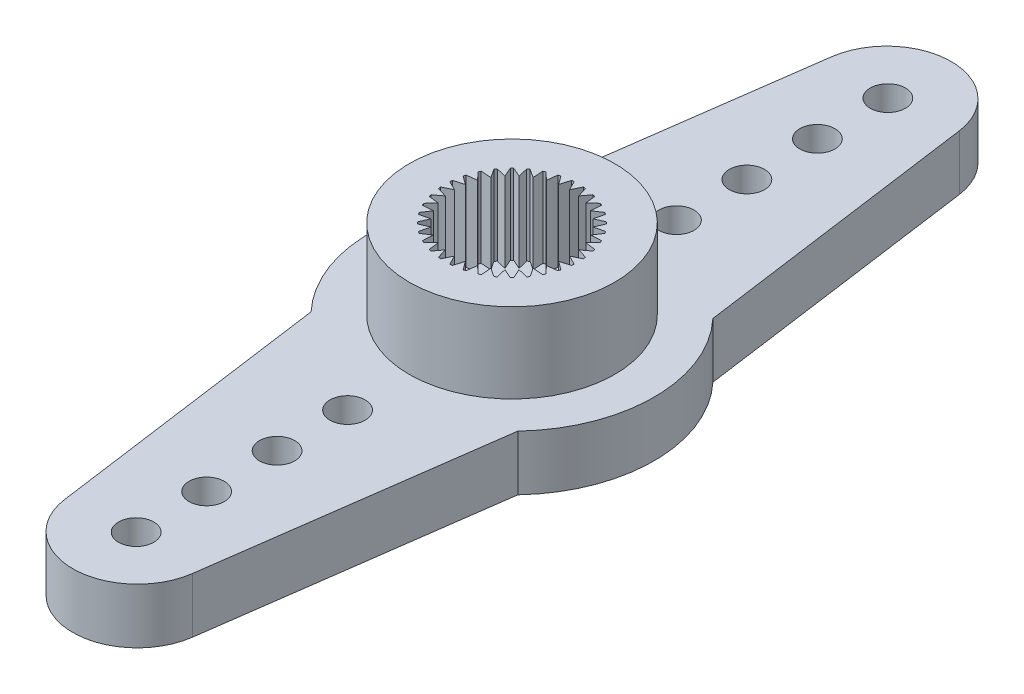
SolidWorks part; units mm, degrees
ref_plane "Front Plane" through (0, 0, 0) normal (0, 0, 1) x (1, 0, 0)
ref_plane "Top Plane" through (0, 0, 0) normal (0, 1, 0) x (1, 0, 0)
ref_plane "Right Plane" through (0, 0, 0) normal (1, 0, 0) x (0, 0, -1)
ref_plane "Plane1" through (0, 2.35, 0) normal (0, 1, 0) x (1, 0, 0)
sketch "Sketch1" plane through (0, 2.35, 0) normal (0, 1, 0) x (1, 0, 0)
  line L0 (2.7243, -16.325) -> (4.4, -4.1524)
  line L1 (4.4, 4.1524) -> (2.7243, 16.325)
  line L2 (-2.7243, 16.325) -> (-4.4, 4.1524)
  line L3 (-4.4, -4.1524) -> (-2.7243, -16.325)
  arc A0 (-2.7243, -16.325) -> (2.7243, -16.325) centre (0, -15.95) ccw
  arc A1 (4.4, -4.1524) -> (4.4, 4.1524) centre (0, 0) ccw
  arc A2 (2.7243, 16.325) -> (-2.7243, 16.325) centre (0, 15.95) ccw
  arc A3 (-4.4, 4.1524) -> (-4.4, -4.1524) centre (0, 0) ccw
extrude "Boss-Extrude1" add sketch "Sketch1" against normal blind 2.35
sketch "Sketch2" plane through (0, 2.35, 0) normal (0, 1, 0) x (-1, 0, 0)
  circle A0 centre (0, 0) radius 4.375
extrude "Boss-Extrude2" add sketch "Sketch2" along normal blind 3.4
sketch "Sketch3" plane through (0, 5.75, 0) normal (0, 1, 0) x (-1, 0, 0)
  line L0 (0.6873, 2.7659) -> (0.4254, 2.4128)
  line L1 (0.4254, 2.4128) -> (0.3001, 2.8342)
  line L2 (0.1966, 2.8432) -> (0, 2.45)
  line L3 (0, 2.45) -> (-0.1966, 2.8432)
  line L4 (-0.3001, 2.8342) -> (-0.4254, 2.4128)
  line L5 (-0.4254, 2.4128) -> (-0.6873, 2.7659)
  line L6 (-0.7877, 2.739) -> (-0.8379, 2.3022)
  line L7 (-0.8379, 2.3022) -> (-1.1572, 2.6045)
  line L8 (-1.2513, 2.5606) -> (-1.225, 2.1218)
  line L9 (-1.225, 2.1218) -> (-1.5919, 2.364)
  line L10 (-1.677, 2.3044) -> (-1.5748, 1.8768)
  line L11 (-1.5748, 1.8768) -> (-1.9782, 2.0517)
  line L12 (-2.0517, 1.9782) -> (-1.8768, 1.5748)
  line L13 (-1.8768, 1.5748) -> (-2.3044, 1.677)
  line L14 (-2.364, 1.5919) -> (-2.1218, 1.225)
  line L15 (-2.1218, 1.225) -> (-2.5606, 1.2513)
  line L16 (-2.6045, 1.1572) -> (-2.3022, 0.8379)
  line L17 (-2.3022, 0.8379) -> (-2.739, 0.7877)
  line L18 (-2.7659, 0.6873) -> (-2.4128, 0.4254)
  line L19 (-2.4128, 0.4254) -> (-2.8342, 0.3001)
  line L20 (-2.8432, 0.1966) -> (-2.45, 0)
  line L21 (-2.45, 0) -> (-2.8432, -0.1966)
  line L22 (-2.8342, -0.3001) -> (-2.4128, -0.4254)
  line L23 (-2.4128, -0.4254) -> (-2.7659, -0.6873)
  line L24 (-2.739, -0.7877) -> (-2.3022, -0.8379)
  line L25 (-2.3022, -0.8379) -> (-2.6045, -1.1572)
  line L26 (-2.5606, -1.2513) -> (-2.1218, -1.225)
  line L27 (-2.1218, -1.225) -> (-2.364, -1.5919)
  line L28 (-2.3044, -1.677) -> (-1.8768, -1.5748)
  line L29 (-1.8768, -1.5748) -> (-2.0517, -1.9782)
  line L30 (-1.9782, -2.0517) -> (-1.5748, -1.8768)
  line L31 (-1.5748, -1.8768) -> (-1.677, -2.3044)
  line L32 (-1.5919, -2.364) -> (-1.225, -2.1218)
  line L33 (-1.225, -2.1218) -> (-1.2513, -2.5606)
  line L34 (-1.1572, -2.6045) -> (-0.8379, -2.3022)
  line L35 (-0.8379, -2.3022) -> (-0.7877, -2.739)
  line L36 (-0.6873, -2.7659) -> (-0.4254, -2.4128)
  line L37 (-0.4254, -2.4128) -> (-0.3001, -2.8342)
  line L38 (-0.1966, -2.8432) -> (0, -2.45)
  line L39 (0, -2.45) -> (0.1966, -2.8432)
  line L40 (0.3001, -2.8342) -> (0.4254, -2.4128)
  line L41 (0.4254, -2.4128) -> (0.6873, -2.7659)
  line L42 (0.7877, -2.739) -> (0.8379, -2.3022)
  line L43 (0.8379, -2.3022) -> (1.1572, -2.6045)
  line L44 (1.2513, -2.5606) -> (1.225, -2.1218)
  line L45 (1.225, -2.1218) -> (1.5919, -2.364)
  line L46 (1.677, -2.3044) -> (1.5748, -1.8768)
  line L47 (1.5748, -1.8768) -> (1.9782, -2.0517)
  line L48 (2.0517, -1.9782) -> (1.8768, -1.5748)
  line L49 (1.8768, -1.5748) -> (2.3044, -1.677)
  line L50 (2.364, -1.5919) -> (2.1218, -1.225)
  line L51 (2.1218, -1.225) -> (2.5606, -1.2513)
  line L52 (2.6045, -1.1572) -> (2.3022, -0.8379)
  line L53 (2.3022, -0.8379) -> (2.739, -0.7877)
  line L54 (2.7659, -0.6873) -> (2.4128, -0.4254)
  line L55 (2.4128, -0.4254) -> (2.8342, -0.3001)
  line L56 (2.8432, -0.1966) -> (2.45, 0)
  line L57 (2.45, 0) -> (2.8432, 0.1966)
  line L58 (2.8342, 0.3001) -> (2.4128, 0.4254)
  line L59 (2.4128, 0.4254) -> (2.7659, 0.6873)
  line L60 (2.739, 0.7877) -> (2.3022, 0.8379)
  line L61 (2.3022, 0.8379) -> (2.6045, 1.1572)
  line L62 (2.5606, 1.2513) -> (2.1218, 1.225)
  line L63 (2.1218, 1.225) -> (2.364, 1.5919)
  line L64 (2.3044, 1.677) -> (1.8768, 1.5748)
  line L65 (1.8768, 1.5748) -> (2.0517, 1.9782)
  line L66 (1.9782, 2.0517) -> (1.5748, 1.8768)
  line L67 (1.5748, 1.8768) -> (1.677, 2.3044)
  line L68 (1.5919, 2.364) -> (1.225, 2.1218)
  line L69 (1.225, 2.1218) -> (1.2513, 2.5606)
  line L70 (1.1572, 2.6045) -> (0.8379, 2.3022)
  line L71 (0.8379, 2.3022) -> (0.7877, 2.739)
  arc A0 (0.3001, 2.8342) -> (0.1966, 2.8432) centre (0, 0) ccw
  arc A1 (-0.1966, 2.8432) -> (-0.3001, 2.8342) centre (0, 0) ccw
  arc A2 (-0.6873, 2.7659) -> (-0.7877, 2.739) centre (0, 0) ccw
  arc A3 (-1.1572, 2.6045) -> (-1.2513, 2.5606) centre (0, 0) ccw
  arc A4 (-1.5919, 2.364) -> (-1.677, 2.3044) centre (0, 0) ccw
  arc A5 (-1.9782, 2.0517) -> (-2.0517, 1.9782) centre (0, 0) ccw
  arc A6 (-2.3044, 1.677) -> (-2.364, 1.5919) centre (0, 0) ccw
  arc A7 (-2.5606, 1.2513) -> (-2.6045, 1.1572) centre (0, 0) ccw
  arc A8 (-2.739, 0.7877) -> (-2.7659, 0.6873) centre (0, 0) ccw
  arc A9 (-2.8342, 0.3001) -> (-2.8432, 0.1966) centre (0, 0) ccw
  arc A10 (-2.8432, -0.1966) -> (-2.8342, -0.3001) centre (0, 0) ccw
  arc A11 (-2.7659, -0.6873) -> (-2.739, -0.7877) centre (0, 0) ccw
  arc A12 (-2.6045, -1.1572) -> (-2.5606, -1.2513) centre (0, 0) ccw
  arc A13 (-2.364, -1.5919) -> (-2.3044, -1.677) centre (0, 0) ccw
  arc A14 (-2.0517, -1.9782) -> (-1.9782, -2.0517) centre (0, 0) ccw
  arc A15 (-1.677, -2.3044) -> (-1.5919, -2.364) centre (0, 0) ccw
  arc A16 (-1.2513, -2.5606) -> (-1.1572, -2.6045) centre (0, 0) ccw
  arc A17 (-0.7877, -2.739) -> (-0.6873, -2.7659) centre (0, 0) ccw
  arc A18 (-0.3001, -2.8342) -> (-0.1966, -2.8432) centre (0, 0) ccw
  arc A19 (0.1966, -2.8432) -> (0.3001, -2.8342) centre (0, 0) ccw
  arc A20 (0.6873, -2.7659) -> (0.7877, -2.739) centre (0, 0) ccw
  arc A21 (1.1572, -2.6045) -> (1.2513, -2.5606) centre (0, 0) ccw
  arc A22 (1.5919, -2.364) -> (1.677, -2.3044) centre (0, 0) ccw
  arc A23 (1.9782, -2.0517) -> (2.0517, -1.9782) centre (0, 0) ccw
  arc A24 (2.3044, -1.677) -> (2.364, -1.5919) centre (0, 0) ccw
  arc A25 (2.5606, -1.2513) -> (2.6045, -1.1572) centre (0, 0) ccw
  arc A26 (2.739, -0.7877) -> (2.7659, -0.6873) centre (0, 0) ccw
  arc A27 (2.8342, -0.3001) -> (2.8432, -0.1966) centre (0, 0) ccw
  arc A28 (2.8432, 0.1966) -> (2.8342, 0.3001) centre (0, 0) ccw
  arc A29 (2.7659, 0.6873) -> (2.739, 0.7877) centre (0, 0) ccw
  arc A30 (2.6045, 1.1572) -> (2.5606, 1.2513) centre (0, 0) ccw
  arc A31 (2.364, 1.5919) -> (2.3044, 1.677) centre (0, 0) ccw
  arc A32 (2.0517, 1.9782) -> (1.9782, 2.0517) centre (0, 0) ccw
  arc A33 (1.677, 2.3044) -> (1.5919, 2.364) centre (0, 0) ccw
  arc A34 (1.2513, 2.5606) -> (1.1572, 2.6045) centre (0, 0) ccw
  arc A35 (0.7877, 2.739) -> (0.6873, 2.7659) centre (0, 0) ccw
extrude "Cut-Extrude1" cut sketch "Sketch3" against normal blind 3.4
hole_wizard "Ø8.8 (8.8) Diameter Hole1" positions "Sketch5" profile "Sketch4" hole size "Ø8.8" standard "ANSI Metric"
sketch "Sketch5" plane through (0, 0, 0) normal (0, -1, 0) x (-1, 0, 0)
  point P0 (0, 0)
sketch "Sketch4" plane through (0, 0, 0) normal (1, 0, 0) x (0, 0, -1)
  line L0 (0, 0) -> (0, 0.3)
  line L1 (0, 0.3) -> (4.4, 0.3)
  line L2 (4.4, 0.3) -> (4.4, 0)
  line L5 (4.4, 0) -> (0, 0)
  line L10 (0, 0.3) -> (-4.4, 0.3) construction
  line L11 (0, -6.35) -> (0, 107.95) construction
  dimension "Hole Dia." = 8.8
  dimension "Hole Depth" = 0.3
  dimension "Drill Angle" = 180
sketch "Sketch6" plane through (0, 0, 0) normal (0, 0, 1) x (1, 0, 0)
  line L0 (3.25, 0.3) -> (0, 0.3)
  line L1 (0, 0.3) -> (0, 0)
  line L2 (0, 0) -> (3.25, 0)
  line L3 (3.25, 0) -> (3.25, 0.3)
  line L4 (0, 0.3) -> (0, 0) construction
revolve "Revolve1" add sketch "Sketch6" angle 360 about L4
hole_wizard "Ø1.5 (1.5) Diameter Hole1" positions "Sketch8" profile "Sketch7" hole size "Ø1.5" standard "ANSI Metric"
sketch "Sketch8" plane through (0, 2.35, 0) normal (0, 1, 0) x (1, 0, 0)
  point P0 (0, -7)
  point P1 (0, 16)
  point P2 (0, -10)
  point P3 (0, -13)
  point P4 (0, -16)
  point P5 (0, 13)
  point P6 (0, 10)
  point P7 (0, 7)
sketch "Sketch7" plane through (0, 2.35, 7) normal (1, 0, 0) x (0, 0, 1)
  line L0 (0, 0) -> (0, 2.35)
  line L1 (0, 2.35) -> (0.75, 2.35)
  line L2 (0.75, 2.35) -> (0.75, 0)
  line L5 (0.75, 0) -> (0, 0)
  line L11 (0, -6.35) -> (0, 107.95) construction
  dimension "Thru Hole Dia." = 1.5
  dimension "Thru Hole Depth" = 2.35
hole_wizard "CBORE for M2.5 Hex Head Machine Screw1" positions "Sketch10" profile "Sketch9" counterbore size "M2.5" standard "ANSI Metric"
sketch "Sketch10" plane through (0, 0, 0) normal (0, -1, 0) x (-1, 0, 0)
  point P0 (0, 0)
sketch "Sketch9" plane through (0, 0, 0) normal (1, 0, 0) x (0, 0, -1)
  line L0 (0, 0) -> (0, 5.75)
  line L1 (0, 5.75) -> (1.5, 5.75)
  line L3 (1.5, 5.75) -> (1.5, 0.3)
  line L4 (1.5, 0.3) -> (2.75, 0.3)
  line L5 (2.75, 0.3) -> (2.75, 0)
  line L7 (2.75, 0) -> (0, 0)
  line L11 (0, -6.35) -> (0, 107.95) construction
  dimension "Thru Hole Dia." = 3
  dimension "Thru Hole Depth" = 5.75
  dimension "C'Bore Dia." = 5.5
  dimension "C'Bore Depth" = 0.3
